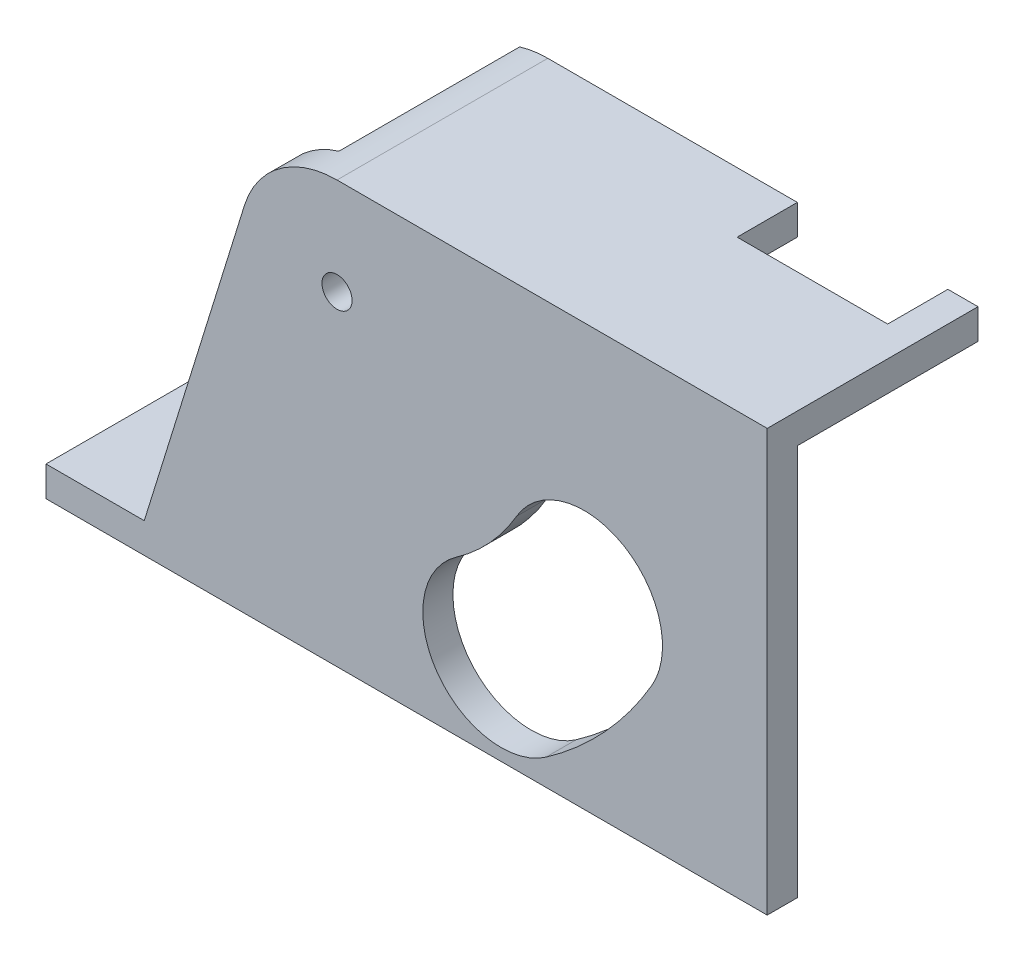
SolidWorks part; units mm, degrees
ref_plane "Front Plane" through (0, 0, 0) normal (0, 0, 1) x (1, 0, 0)
ref_plane "Top Plane" through (0, 0, 0) normal (0, 1, 0) x (1, 0, 0)
ref_plane "Right Plane" through (0, 0, 0) normal (1, 0, 0) x (0, 0, -1)
sketch "Sketch1" plane through (0, 0, 0) normal (0, 0, 1) x (1, 0, 0)
  line L1 (0, 0) -> (120, 0)
  line L2 (0, 0) -> (0, 100)
  line L3 (0, 100) -> (120, 100)
  line L4 (120, 0) -> (120, 100)
  dimension "D1" = 120
  dimension "D2" = 100
extrude "Boss-Extrude1" add sketch "Sketch1" along normal blind 5
sketch "Sketch2" plane through (0, 0, 5) normal (0, 0, 1) x (1, 0, 0)
  line L0 (0, 0) -> (120, 0) construction
  line L3 (83.2628, 4.351) -> (120, 30.0747) construction
  line L4 (120, 0) -> (120, 100) construction
  arc A0 (75.8063, 15) -> (89.605, 30) centre (48.5614, 53.9097) ccw construction
  arc A1 (83.2628, 4.351) -> (100.8379, 23.4563) centre (48.5614, 53.9097) ccw
  arc A2 (68.3498, 25.649) -> (78.372, 36.5437) centre (48.5614, 53.9097) ccw
  arc A3 (68.3498, 25.649) -> (83.2628, 4.351) centre (75.8063, 15) ccw
  arc A4 (100.8379, 23.4563) -> (78.372, 36.5437) centre (89.605, 30) ccw
  arc A5 (48.5614, 6.4097) -> (89.605, 30) centre (48.5614, 53.9097) ccw construction
  arc A6 (48.5614, -28.5903) -> (119.8476, 12.3823) centre (48.5614, 53.9097) ccw construction
  arc A7 (48.5614, 41.4097) -> (59.3623, 47.6177) centre (48.5614, 53.9097) ccw construction
  arc A8 (48.5614, 41.4097) -> (48.5614, -28.5903) centre (48.5614, 6.4097) ccw construction
  arc A9 (119.8476, 12.3823) -> (59.3623, 47.6177) centre (89.605, 30) ccw construction
  circle A10 centre (48.5614, 53.9097) radius 2.5
  point P3 (83.5196, 21.7512)
  point P17 (72.2314, 12.7274)
  point P27 (115, 5)
  dimension "D1" = 47.5
  dimension "D3" = 13
  dimension "D6" = 5
  dimension "D5" = 35
  dimension "D9" = 5
  dimension "D2" = 15
  dimension "D4" = 30
  dimension "D7" = 5
  dimension "D8" = 35
extrude "Cut-Extrude1" cut sketch "Sketch2" against normal through all
sketch "Sketch3" plane through (0, 0, 0) normal (0, 0, -1) x (-1, 0, 0)
  line L0 (0, 100) -> (0, 0) construction
  line L1 (-120, 0) -> (0, 0)
  line L2 (-120, 0) -> (-120, 1.6)
  line L3 (-120, 1.6) -> (0, 1.6)
  line L4 (0, 0) -> (0, 1.6)
  dimension "D1" = 1.6
extrude "Boss-Extrude2" [suppressed] add sketch "Sketch3" along normal blind 30
sketch "Sketch4" plane through (0, 0, 5) normal (0, 0, 1) x (1, 0, 0)
  line L0 (89.605, 30) -> (48.5614, 53.9097) construction
  line L1 (48.5614, 53.9097) -> (75.8063, 15) construction
  line L2 (92.6251, 35.1845) -> (51.5816, 59.0942) construction
  line L3 (52.6571, 56.7776) -> (79.902, 17.8679) construction
  line L4 (120, 0) -> (120, 100) construction
  line L5 (0, 0) -> (120, 0) construction
  arc A0 (65.8054, 38) -> (73, 46.617) centre (63.0497, 47.6128) ccw construction
  arc A1 (66.4943, 35.5968) -> (75.4876, 46.368) centre (63.0497, 47.6128) ccw
  arc A2 (65.1165, 40.4032) -> (70.5124, 46.8659) centre (63.0497, 47.6128) ccw
  arc A3 (65.1165, 40.4032) -> (66.4943, 35.5968) centre (65.8054, 38) ccw
  arc A4 (75.4876, 46.368) -> (70.5124, 46.8659) centre (73, 46.617) ccw
  point P13 (70.7259, 41.2037)
  dimension "D3" = 2.5
  dimension "D4" = 10
  dimension "D5" = 47
  dimension "D6" = 38
  dimension "D1" = 6
  dimension "D2" = 5
extrude "Cut-Extrude2" [suppressed] cut sketch "Sketch4" against normal through all
sketch "Sketch5" plane through (0, 0, 5) normal (0, 0, 1) x (1, 0, 0)
  line L0 (120, 70) -> (48.5614, 70)
  line L1 (120, 0) -> (120, 100) construction
  line L2 (33.1929, 58.6749) -> (15, 0)
  line L3 (0, 0) -> (120, 0) construction
  line L4 (15, 0) -> (0, 0)
  line L5 (0, 0) -> (0, 100)
  line L6 (0, 100) -> (120, 100)
  line L7 (120, 100) -> (120, 70)
  arc A0 (48.5614, 70) -> (33.1929, 58.6749) centre (48.5614, 53.9097) ccw
  circle A1 centre (48.5614, 53.9097) radius 2.5 construction
  dimension "D1" = 15
  dimension "D2" = 30
extrude "Cut-Extrude3" cut sketch "Sketch5" against normal blind 10
sketch "Sketch7" plane through (0, 0, 0) normal (0, 0, -1) x (-1, 0, 0)
  line L0 (-15, 0) -> (-32.773, 57.3206)
  line L1 (-120, 70) -> (-48.5614, 70)
  line L2 (-120, 70) -> (-120, 65)
  line L3 (-120, 65) -> (-48.5614, 65)
  line L5 (-33.1929, 58.6749) -> (-15, 0) construction
  line L7 (-37.207, 54.7377) -> (-20.2348, 0)
  line L8 (-15, 0) -> (-120, 0) construction
  line L9 (-20.2348, 0) -> (-15, 0)
  line L10 (-89.605, 30) -> (-48.5614, 53.9097) construction
  line L11 (-48.5614, 53.9097) -> (-29.5237, 65) construction
  line L12 (-75.8063, 15) -> (-48.5614, 53.9097) construction
  line L13 (-48.5614, 53.9097) -> (-34.8806, 73.4479) construction
  line L14 (-79.902, 17.8679) -> (-52.6571, 56.7776) construction
  line L15 (-52.6571, 56.7776) -> (-38.9763, 76.3158) construction
  line L16 (-87.0882, 25.6796) -> (-46.0446, 49.5893) construction
  line L17 (-46.0446, 49.5893) -> (-27.0069, 60.6796) construction
  line L18 (-47.0357, 64.8058) -> (-43.885, 69.3055)
  line L19 (-37.207, 54.7377) -> (-32.773, 57.3206)
  arc A0 (-48.5614, 70) -> (-43.885, 69.3055) centre (-48.5614, 53.9097) cw
  arc A1 (-33.1929, 58.6749) -> (-48.5614, 70) centre (-48.5614, 53.9097) ccw construction
  arc A2 (-48.5614, 65) -> (-47.0357, 64.8058) centre (-48.5614, 58.9097) cw
  dimension "D1" = 5
  dimension "D2" = 5
  dimension "D4" = 5
  dimension "D5" = 5
  dimension "D6" = 5
extrude "Boss-Extrude3" add sketch "Sketch7" along normal blind 30
sketch "Sketch8" plane through (0, 0, -30) normal (0, 0, -1) x (-1, 0, 0)
  line L0 (-20.2348, 0) -> (-15, 0) construction
  line L1 (-20.2348, 0) -> (-0.2348, 0)
  line L2 (-20.2348, 0) -> (-20.2348, 5)
  line L3 (-20.2348, 5) -> (-0.2348, 5)
  line L4 (-0.2348, 0) -> (-0.2348, 5)
  line L5 (-37.207, 54.7377) -> (-20.2348, 0) construction
  point P8 (0, 0)
  dimension "D1" = 20
  dimension "D2" = 5
extrude "Boss-Extrude4" add sketch "Sketch8" against normal through all
sketch "Sketch9" plane through (0, 70, 0) normal (0, 1, 0) x (1, 0, 0)
  line L1 (115, 30) -> (90, 30)
  line L2 (115, 30) -> (115, 20)
  line L3 (115, 20) -> (90, 20)
  line L4 (90, 30) -> (90, 20)
  line L5 (120, 30) -> (120, -5) construction
  line L6 (48.5614, 30) -> (120, 30) construction
  dimension "D1" = 10
  dimension "D3" = 25
  dimension "D4" = 5
extrude "Cut-Extrude4" cut sketch "Sketch9" against normal through all
